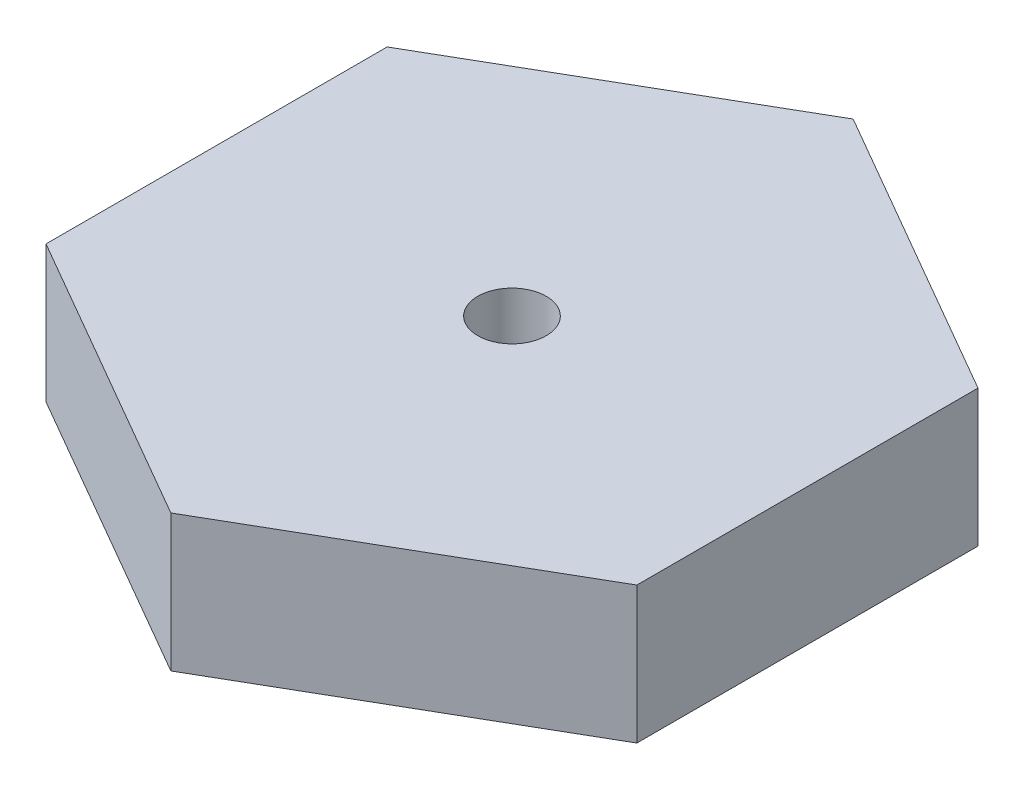
SolidWorks part; units mm, degrees
ref_plane "Front Plane" through (0, 0, 0) normal (0, 0, 1) x (1, 0, 0)
ref_plane "Top Plane" through (0, 0, 0) normal (0, 1, 0) x (1, 0, 0)
ref_plane "Right Plane" through (0, 0, 0) normal (1, 0, 0) x (0, 0, -1)
sketch "Sketch1" plane through (0, 0, 0) normal (0, 1, 0) x (1, 0, 0)
  line L1 (0, 12.6629) -> (-10.9664, 6.3314)
  line L2 (-10.9664, 6.3314) -> (-10.9664, -6.3314)
  line L3 (-10.9664, -6.3314) -> (0, -12.6629)
  line L4 (0, -12.6629) -> (10.9664, -6.3314)
  line L5 (10.9664, -6.3314) -> (10.9664, 6.3314)
  line L6 (10.9664, 6.3314) -> (0, 12.6629)
  circle A1 centre (0, 0) radius 1.27
  circle A3 centre (0, 0) radius 10.9664 construction
extrude "Boss-Extrude4" add sketch "Sketch1" along normal blind 5.08
